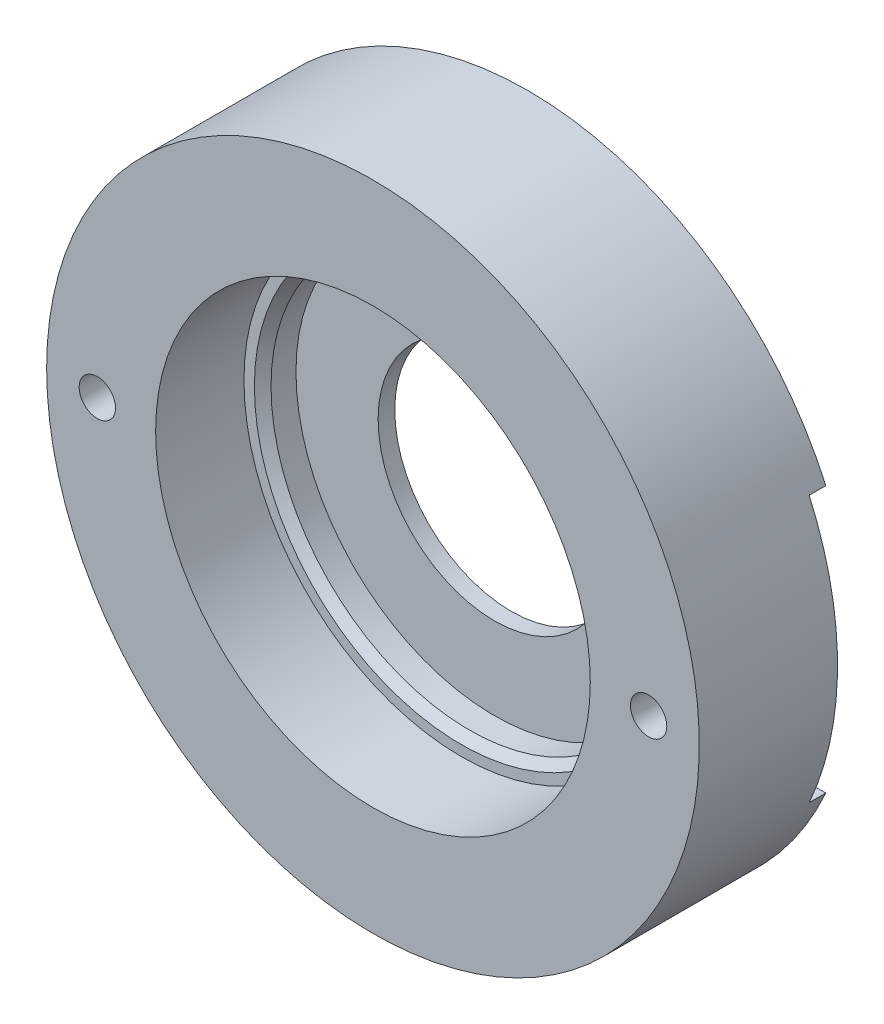
SolidWorks part; units mm, degrees
ref_plane "Front Plane" through (0, 0, 0) normal (0, 0, 1) x (1, 0, 0)
ref_plane "Top Plane" through (0, 0, 0) normal (0, 1, 0) x (1, 0, 0)
ref_plane "Right Plane" through (0, 0, 0) normal (1, 0, 0) x (0, 0, -1)
sketch "Sketch1" plane through (0, 0, 0) normal (0, 1, 0) x (1, 0, 0)
  line L0 (0, 25.4113) -> (0, -24.5124) construction
  line L2 (-7, 3.5255) -> (-19.6178, 3.5255)
  line L3 (-7, 3.5255) -> (-7, 1.5255)
  line L4 (-7, 1.5255) -> (-19.6178, 1.5255)
  line L5 (-19.6178, 3.5255) -> (-19.6178, 1.5255)
  line L6 (-11.938, 1.5255) -> (-19.6178, 1.5255)
  line L7 (-11.938, 1.5255) -> (-11.938, -0.4745)
  line L8 (-11.938, -0.4745) -> (-19.6178, -0.4745)
  line L9 (-19.6178, 1.5255) -> (-19.6178, -0.4745)
  line L10 (-13.0646, -0.4745) -> (-19.6178, -0.4745)
  line L11 (-13.0646, -0.4745) -> (-13.0646, -5.7845)
  line L12 (-13.0646, -5.7845) -> (-19.6178, -5.7845)
  line L13 (-19.6178, -0.4745) -> (-19.6178, -5.7845)
  dimension "D1" = 7
  dimension "D2" = 2
  dimension "D3" = 2
  dimension "D4" = 5.31
  dimension "D5" = 11.938
  dimension "D6" = 6.5532
revolve "Revolve1" add sketch "Sketch1" angle 360 about L0
sketch "Sketch2" plane through (0, 0, -3.5255) normal (0, 0, -1) x (-1, 0, 0)
  line L0 (-19.6178, 0) -> (19.6178, 0) construction
  line L1 (0, -19.6178) -> (0, 19.6178) construction
  circle A0 centre (0, 0) radius 19.6178 construction
  circle A1 centre (16.57, 0) radius 1.0922
  circle A2 centre (-16.57, 0) radius 1.0922
  point P11 (0, 0)
  dimension "D1" = 2.1844
  dimension "D3" = 16.57
extrude "Cut-Extrude1" cut sketch "Sketch2" against normal through all
sketch "Sketch3" plane through (0, 0, -3.5255) normal (0, 0, -1) x (-1, 0, 0)
  line L0 (19.6178, 0) -> (-19.6178, 0) construction
  line L1 (0, 19.6178) -> (0, -19.6178) construction
  line L3 (-22.5619, 8) -> (22.5619, 8)
  line L4 (-22.5619, 8) -> (-22.5619, -8)
  line L5 (-22.5619, -8) -> (22.5619, -8)
  line L6 (22.5619, 8) -> (22.5619, -8)
  line L7 (-22.5619, 8) -> (22.5619, -8) construction
  line L8 (-22.5619, -8) -> (22.5619, 8) construction
  circle A0 centre (0, 0) radius 19.6178 construction
  point P7 (0, 0)
  dimension "D1" = 16
extrude "Cut-Extrude2" cut sketch "Sketch3" against normal blind 1
chamfer "Chamfer1" distance 0.5 angle 45 1 edges at (-11.938, 0, 0.4745)
